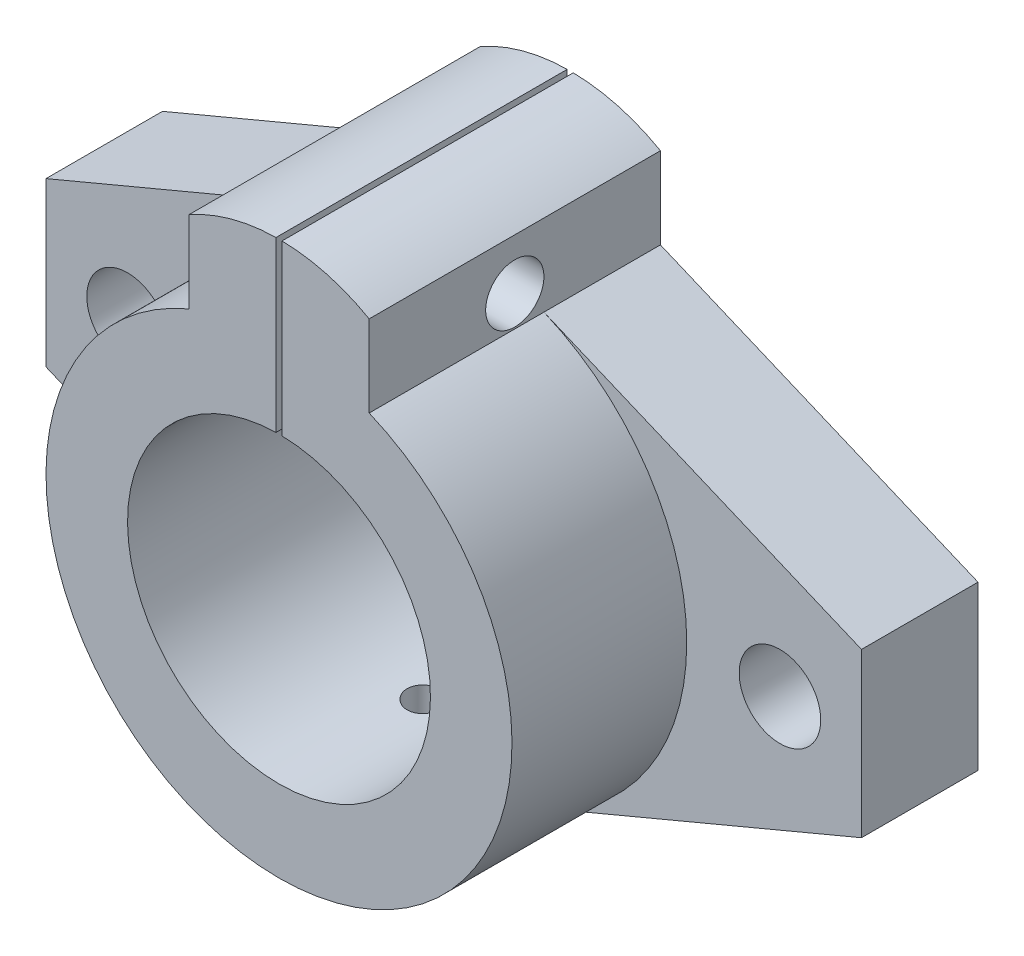
SolidWorks part; units mm, degrees
material "6061 合金"
ref_plane "前视基准面" through (0, 0, 0) normal (0, 0, 1) x (1, 0, 0)
ref_plane "上视基准面" through (0, 0, 0) normal (0, 1, 0) x (1, 0, 0)
ref_plane "右视基准面" through (0, 0, 0) normal (1, 0, 0) x (0, 0, -1)
sketch "草图1" plane through (0, 0, 0) normal (0, 0, 1) x (1, 0, 0)
  line L0 (-7.7403, 18.4415) -> (-7.7403, 25.4415)
  line L1 (-35, -7) -> (-35, 7)
  line L2 (-35, 7) -> (-7.7403, 18.4415)
  line L3 (-35, -7) -> (-7.7403, -18.4415)
  line L4 (7.7403, 18.4415) -> (7.7403, 25.4415)
  line L5 (35, -7) -> (7.7403, -18.4415)
  line L6 (35, -7) -> (35, 7)
  line L7 (35, 7) -> (7.7403, 18.4415)
  line L8 (0, 0) -> (-28, 0) construction
  circle A0 centre (0, 0) radius 13
  arc A1 (-7.7403, 18.4415) -> (7.7403, 18.4415) centre (0, 0) ccw
  arc A2 (-7.7403, 25.4415) -> (7.7403, 25.4415) centre (0, 11.8749) cw
  circle A3 centre (-28, 0) radius 3.5
  circle A4 centre (28, 0) radius 3.5
  dimension "D1" = 28
  dimension "D3" = 26
  dimension "D4" = 20
  dimension "D5" = 7
  dimension "D6" = 7
  dimension "D2" = 28
  dimension "D7" = 70
extrude "凸台-拉伸2" add sketch "草图1" along normal blind 10 contours A1 L5 L6 L7 | A2 L0 A1 L4 A0 | A1 L2 L1 L3
sketch "草图2" plane through (0, 0, 10) normal (0, 0, 1) x (1, 0, 0)
  line L0 (-7.7403, 18.4415) -> (-7.7403, 25.4415)
  line L1 (7.7403, 18.4415) -> (7.7403, 25.4415)
  circle A0 centre (0, 0) radius 13
  arc A1 (-7.7403, 18.4415) -> (7.7403, 18.4415) centre (0, 0) ccw
  arc A2 (-7.7403, 25.4415) -> (7.7403, 25.4415) centre (0, 11.8749) cw
extrude "凸台-拉伸3" add sketch "草图2" along normal blind 15
sketch "草图3" plane through (0, 0, 25) normal (0, 0, 1) x (1, 0, 0)
  line L1 (-0.2586, 12.3781) -> (-0.2586, 31.1043)
  line L2 (0.2586, 12.3781) -> (0.2586, 31.1043)
  line L3 (-0.2586, 12.3781) -> (0.2586, 12.3781)
  line L4 (-0.2586, 31.1043) -> (0.2586, 31.1043)
extrude "切除-拉伸1" cut sketch "草图3" against normal through all
sketch "草图4" plane through (7.7403, 0, 0) normal (1, 0, 0) x (0, 0, -1)
  circle A0 centre (-12.5, 21.0864) radius 2.5
extrude "切除-拉伸2" cut sketch "草图4" against normal through all
sketch "草图5" plane through (0, 0, 0) normal (0, 1, 0) x (1, 0, 0)
  line L0 (0, 0) -> (0, -25) construction
  line L1 (7.7403, 0) -> (-7.7403, 0) construction
  line L2 (-20, -25) -> (20, -25) construction
  circle A0 centre (0, -12.5) radius 1.5
  dimension "D1" = 3
  dimension "D2" = 12.5
extrude "切除-拉伸3" cut sketch "草图5" against normal through all
